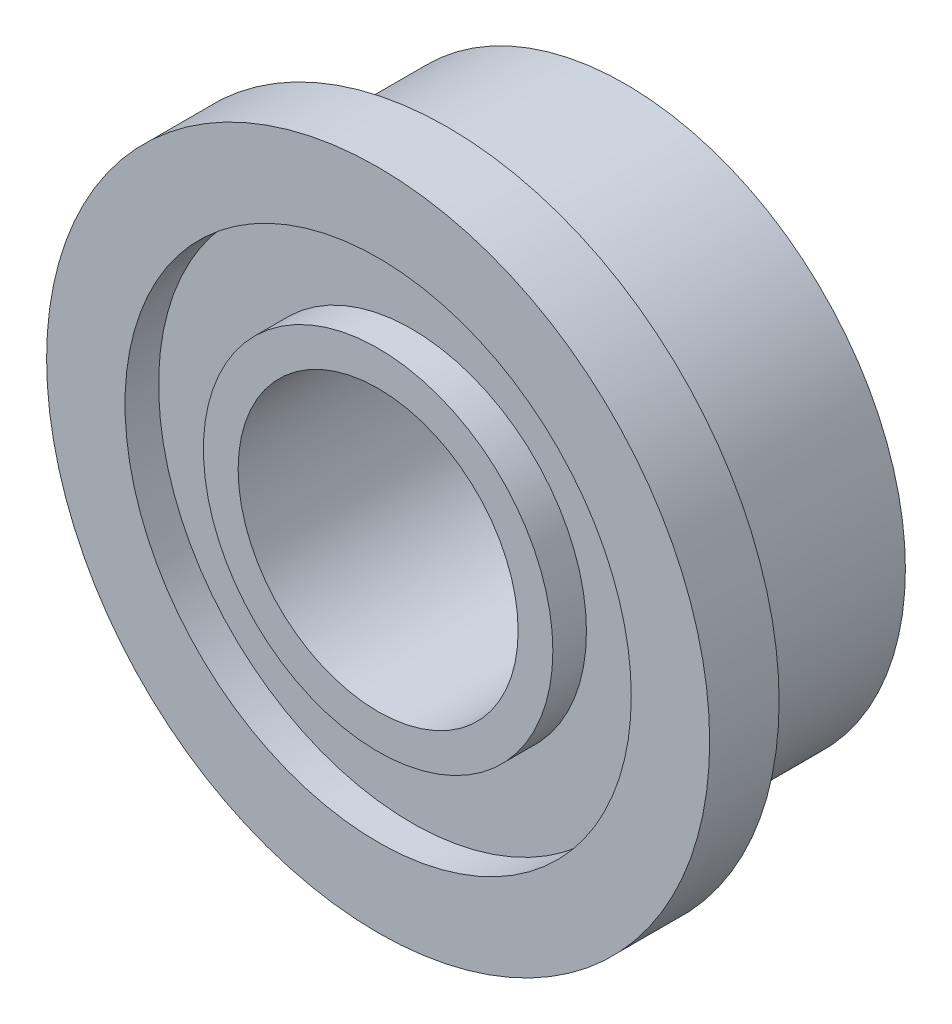
SolidWorks part; units mm, degrees
material "AISI 316 Stainless Steel Sheet (SS)"
ref_plane "Front Plane" through (0, 0, 0) normal (0, 0, 1) x (1, 0, 0)
ref_plane "Top Plane" through (0, 0, 0) normal (0, 1, 0) x (1, 0, 0)
ref_plane "Right Plane" through (0, 0, 0) normal (1, 0, 0) x (0, 0, -1)
sketch "Sketch1" plane through (0, 0, 0) normal (0, 0, 1) x (1, 0, 0)
  circle A0 centre (0, 0) radius 3.175
  circle A1 centre (0, 0) radius 1.5875
  dimension "D1" = 3.175
  dimension "D2" = 6.35
extrude "Boss-Extrude1" add sketch "Sketch1" along normal blind 2.0161
sketch "Sketch2" plane through (0, 0, 2.0161) normal (0, 0, 1) x (1, 0, 0)
  circle A0 centre (0, 0) radius 3.7592
  circle A1 centre (0, 0) radius 1.5875
  circle A2 centre (0, 0) radius 1.5875 construction
  dimension "D1" = 7.5184
extrude "Boss-Extrude2" add sketch "Sketch2" along normal blind 0.7874
sketch "Sketch3" plane through (0, 0, 2.8035) normal (0, 0, 1) x (1, 0, 0)
  circle A0 centre (0, 0) radius 2.8702
  circle A1 centre (0, 0) radius 1.9812
  circle A2 centre (0, 0) radius 1.5875 construction
  circle A3 centre (0, 0) radius 3.7592 construction
  dimension "D1" = 0.3937
  dimension "D2" = 0.889
extrude "Cut-Extrude1" cut sketch "Sketch3" against normal blind 0.381
